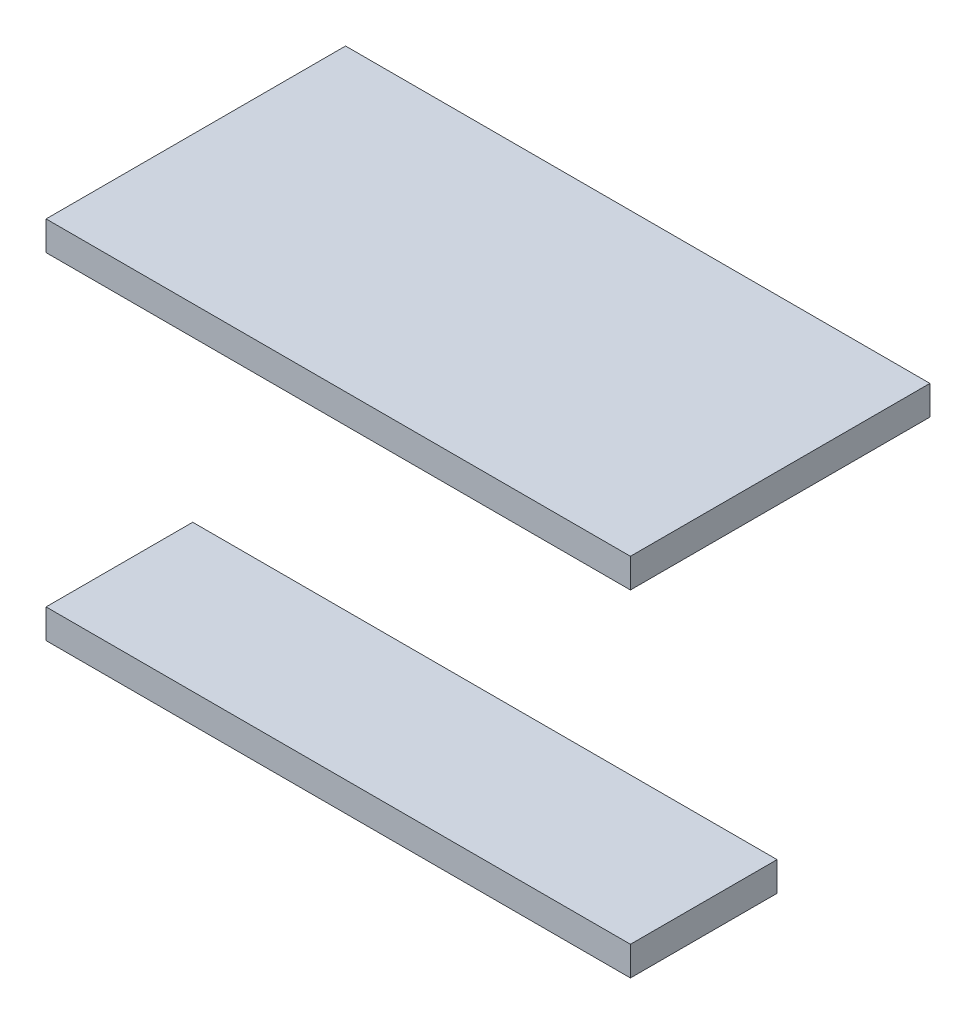
SolidWorks part; units mm, degrees
ref_plane "Front Plane" through (0, 0, 0) normal (0, 0, 1) x (1, 0, 0)
ref_plane "Top Plane" through (0, 0, 0) normal (0, 1, 0) x (1, 0, 0)
ref_plane "Right Plane" through (0, 0, 0) normal (1, 0, 0) x (0, 0, -1)
sketch "Sketch1" plane through (0, 0, 0) normal (1, 0, 0) x (0, 0, -1)
  line L10 (135, 0) -> (135, -12)
  line L14 (12, -138) -> (72.2242, -138)
  line L16 (12, -12) -> (135, -12)
  line L17 (72.2242, -138) -> (72.2242, -150)
  line L18 (12, -138) -> (12, -150)
  line L19 (12, -12) -> (12, 0)
  line L20 (12, 0) -> (135, 0)
  line L21 (12, -150) -> (72.2242, -150)
extrude "Boss-Extrude1" add sketch "Sketch1" against normal blind 240
